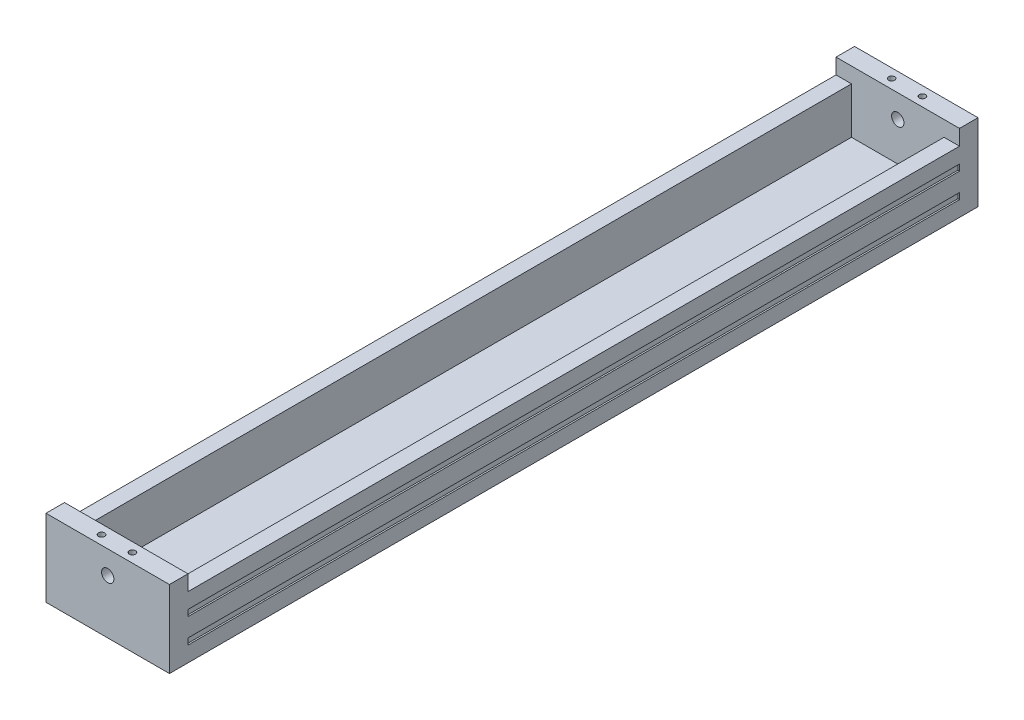
SolidWorks part; units mm, degrees
ref_plane "Front Plane" through (0, 0, 0) normal (0, 0, 1) x (1, 0, 0)
ref_plane "Top Plane" through (0, 0, 0) normal (0, 1, 0) x (1, 0, 0)
ref_plane "Right Plane" through (0, 0, 0) normal (1, 0, 0) x (0, 0, -1)
sketch "Croquis1" plane through (0, 0, 0) normal (0, 0, 1) x (1, 0, 0)
  line L1 (-40, 25) -> (40, 25)
  line L2 (-40, 25) -> (-40, -25)
  line L3 (-40, -25) -> (40, -25)
  line L4 (40, 25) -> (40, -25)
  dimension "D1" = 40
  dimension "D2" = 25
  dimension "D3" = 40
  dimension "D4" = 25
extrude "Saliente-Extruir1" add sketch "Croquis1" along normal blind 12
sketch "Croquis2" plane through (0, 25, 0) normal (0, 1, 0) x (1, 0, 0)
  line L0 (-40, -12) -> (-40, 0) construction
  line L1 (40, -12) -> (40, 0) construction
  line L2 (40, -12) -> (-40, -12) construction
  circle A0 centre (-10, -6) radius 2
  circle A1 centre (10, -6) radius 2
  dimension "D3" = 4
  dimension "D4" = 4
  dimension "D5" = 6
  dimension "D1" = 30
  dimension "D2" = 30
  dimension "D6" = 6
extrude "Cortar-Extruir1" cut sketch "Croquis2" against normal blind 3
sketch "Croquis3" plane through (0, 0, 0) normal (0, 0, -1) x (-1, 0, 0)
  line L0 (40, 25) -> (40, -25) construction
  line L1 (-40, -25) -> (40, -25)
  line L2 (-40, -25) -> (-40, 15)
  line L3 (-40, 15) -> (40, 15)
  line L4 (40, -25) -> (40, 15)
  dimension "D1" = 40
extrude "Saliente-Extruir2" add sketch "Croquis3" along normal blind 500
sketch "Croquis4" plane through (0, 15, 0) normal (0, 1, 0) x (1, 0, 0)
  line L0 (-40, 500) -> (40, 500) construction
  line L1 (-30, 500) -> (30, 500)
  line L2 (-30, 500) -> (-30, 0)
  line L3 (-30, 0) -> (30, 0)
  line L4 (30, 500) -> (30, 0)
  line L5 (-40, 500) -> (-40, 0) construction
  line L6 (40, 500) -> (40, 0) construction
  line L7 (40, -12) -> (-40, -12) construction
  dimension "D1" = 10
  dimension "D2" = 10
  dimension "D3" = 12
extrude "Cortar-Extruir2" cut sketch "Croquis4" against normal blind 30
sketch "Croquis5" plane through (-40, 0, 0) normal (-1, 0, 0) x (0, 0, 1)
  line L0 (-500, -25) -> (-500, 15) construction
  line L2 (-500, 5) -> (-500, 1)
  line L6 (0, 1) -> (-500, 1)
  line L12 (0, -15) -> (0, -11)
  line L13 (0, 5) -> (0, 1)
  line L14 (0, 5) -> (-500, 5)
  line L15 (-500, 5) -> (-500, 1)
  line L16 (-500, 15) -> (0, 15) construction
  line L17 (-500, -5) -> (-482.1517, -5) construction
  line L18 (-500, -15) -> (-500, -11)
  line L19 (0, -15) -> (-500, -15)
  line L20 (0, -11) -> (-500, -11)
  line M7 (-500, 15) -> (-500, -25)
  dimension "D1" = 4
  dimension "D3" = 10
extrude "Cortar-Extruir3" cut sketch "Croquis5" against normal blind 1 contours L13 L14 L6 M7 | L12 L20 L19 M7
sketch "Croquis6" plane through (40, 0, 0) normal (1, 0, 0) x (0, 0, -1)
  line L0 (500, 15) -> (500, -25) construction
  line L1 (500, 5) -> (0, 5)
  line L2 (500, 5) -> (500, 1)
  line L3 (500, 1) -> (0, 1)
  line L4 (0, 5) -> (0, 1)
  line L5 (-12, -25) -> (500, -25) construction
  line L6 (0, -11) -> (500, -11)
  line L7 (0, -11) -> (0, -15)
  line L8 (0, -15) -> (500, -15)
  line L9 (500, -11) -> (500, -15)
  line L10 (500, 15) -> (0, 15) construction
  dimension "D1" = 4
  dimension "D2" = 4
  dimension "D3" = 10
  dimension "D4" = 10
extrude "Cortar-Extruir4" cut sketch "Croquis6" against normal blind 1
ref_plane "Plano1" through (0, 0, -250) normal (0, 0, -1) x (-1, 0, 0)
mirror "Simetría1" about plane through (0, 0, -250) normal (0, 0, -1) of "Cortar-Extruir1", "Saliente-Extruir1"
sketch "Croquis7" plane through (0, 0, -512) normal (0, 0, -1) x (-1, 0, 0)
  line L2 (-40, -25) -> (-40, 25) construction
  line L3 (40, -25) -> (-40, -25) construction
  circle A1 centre (0, 10) radius 4
  dimension "D1" = 40
  dimension "D2" = 8
  dimension "D3" = 35
extrude "Cortar-Extruir5" cut sketch "Croquis7" against normal blind 621
